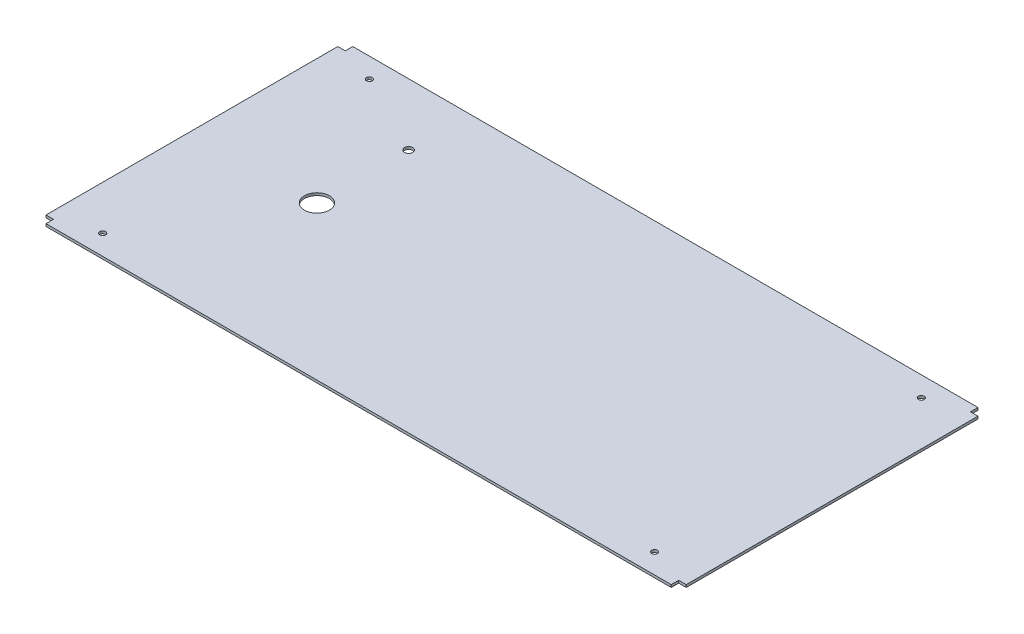
SolidWorks part; units mm, degrees
material "AISI 304"
ref_plane "Front Plane" through (0, 0, 0) normal (0, 0, 1) x (1, 0, 0)
ref_plane "Top Plane" through (0, 0, 0) normal (0, 1, 0) x (1, 0, 0)
ref_plane "Right Plane" through (0, 0, 0) normal (1, 0, 0) x (0, 0, -1)
sketch "Sketch2" plane through (0, 0, 0) normal (0, 1, 0) x (1, 0, 0)
  line L1 (-375, 184) -> (375, 184)
  line L2 (-384, 175) -> (-384, -175)
  line L3 (-375, -184) -> (375, -184)
  line L4 (384, 175) -> (384, -175)
  line L7 (-384, 175) -> (-375, 175)
  line L8 (-375, 184) -> (-375, 175)
  line L11 (-384, -175) -> (-375, -175)
  line L12 (-375, -184) -> (-375, -175)
  line L15 (384, 175) -> (375, 175)
  line L16 (375, 184) -> (375, 175)
  line L19 (384, -175) -> (375, -175)
  line L20 (375, -184) -> (375, -175)
  circle A0 centre (-331.06, 160) radius 3.5
  circle A1 centre (-331.06, -160) radius 3.5
  circle A2 centre (331.06, 160) radius 3.5
  circle A3 centre (331.06, -160) radius 3.5
  point P0 (0, 0)
  point P7 (384, 0)
  point P8 (0, 184)
  dimension "D9" = 7
  dimension "D1" = 768
  dimension "D2" = 368
  dimension "D3" = 9
  dimension "D4" = 9
  dimension "D5" = 52.94
  dimension "D6" = 52.94
  dimension "D7" = 24
  dimension "D8" = 24
extrude "Boss-Extrude1" add sketch "Sketch2" along normal blind 3
sketch "Sketch3" plane through (0, 3, 0) normal (0, 1, 0) x (1, 0, 0)
  line L0 (-384, 175) -> (-384, -175) construction
  circle A0 centre (-234, 0) radius 15
  dimension "D1" = 30
  dimension "D2" = 150
extrude "Cut-Extrude1" cut sketch "Sketch3" against normal through all
sketch "Sketch4" plane through (0, 3, 0) normal (0, 1, 0) x (1, 0, 0)
  line L0 (-384, 175) -> (-384, -175) construction
  circle A0 centre (-234, 110) radius 5
  dimension "D1" = 10
  dimension "D2" = 110
  dimension "D3" = 150
extrude "Cut-Extrude2" cut sketch "Sketch4" against normal through all
